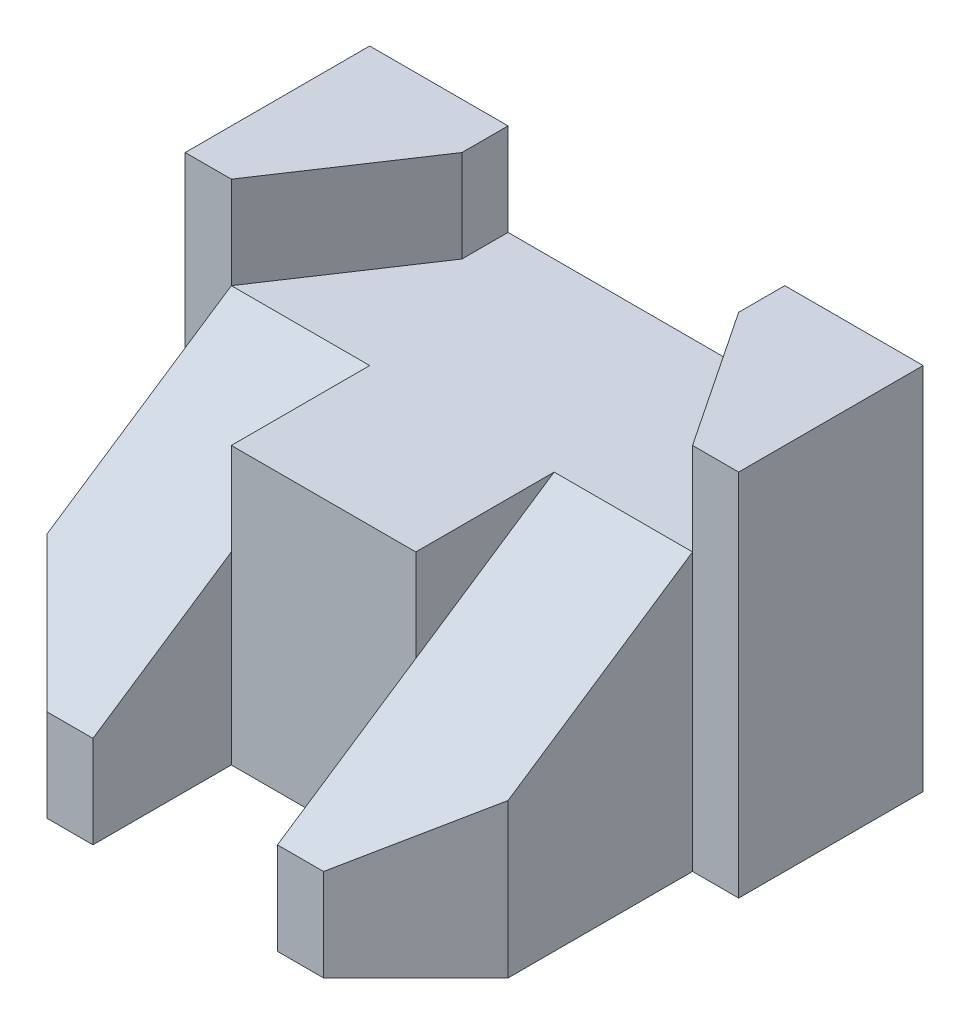
SolidWorks part; units mm, degrees
ref_plane "Front Plane" through (0, 0, 0) normal (0, 0, 1) x (1, 0, 0)
ref_plane "Top Plane" through (0, 0, 0) normal (0, 1, 0) x (1, 0, 0)
ref_plane "Right Plane" through (0, 0, 0) normal (1, 0, 0) x (0, 0, -1)
sketch "Sketch1" plane through (0, 0, 0) normal (0, 1, 0) x (1, 0, 0)
  line L1 (0, 0) -> (120, 0)
  line L2 (0, 0) -> (0, 100)
  line L3 (0, 100) -> (120, 100)
  line L4 (120, 0) -> (120, 100)
  dimension "D1" = 120
  dimension "D2" = 100
extrude "Boss-Extrude1" add sketch "Sketch1" along normal blind 80
sketch "Sketch2" plane through (0, 80, 0) normal (0, 1, 0) x (1, 0, 0)
  line L0 (0, 0) -> (120, 0) construction
  line L1 (80, 0) -> (40, 0)
  line L2 (80, 0) -> (80, 30)
  line L3 (80, 30) -> (40, 30)
  line L4 (40, 0) -> (40, 30)
  dimension "D1" = 40
  dimension "D2" = 30
  dimension "D3" = 40
extrude "Cut-Extrude1" cut sketch "Sketch2" against normal blind 80
sketch "Sketch3" plane through (0, 80, 0) normal (0, 1, 0) x (1, 0, 0)
  line L0 (0, 60) -> (10, 60)
  line L1 (0, 100) -> (0, 0) construction
  line L2 (10, 60) -> (10, 20)
  line L3 (10, 20) -> (30, 0)
  line L4 (0, 0) -> (40, 0) construction
  line L5 (30, 0) -> (0, 0)
  line L6 (0, 0) -> (0, 60)
  line L7 (120, 60) -> (110, 60)
  line L8 (120, 0) -> (120, 100) construction
  line L9 (110, 60) -> (110, 20)
  line L10 (110, 20) -> (90, 0)
  line L11 (80, 0) -> (120, 0) construction
  line L12 (90, 0) -> (120, 0)
  line L13 (120, 0) -> (120, 60)
  dimension "D1" = 10
  dimension "D2" = 40
  dimension "D3" = 60
  dimension "D4" = 20
  dimension "D5" = 20
  dimension "D6" = 10
  dimension "D7" = 40
  dimension "D8" = 20
  dimension "D9" = 20
  dimension "D10" = 10
extrude "Cut-Extrude2" cut sketch "Sketch3" against normal blind 80
sketch "Sketch4" plane through (0, 80, 0) normal (0, 1, 0) x (1, 0, 0)
  line L0 (30, 100) -> (90, 100)
  line L1 (120, 100) -> (0, 100) construction
  line L2 (90, 100) -> (90, 90)
  line L3 (40, 60) -> (10.001, 60)
  line L4 (10.001, 60) -> (30, 90)
  line L5 (80, 60) -> (80, 30)
  line L6 (80, 30) -> (40, 30)
  line L7 (40, 30) -> (40, 60)
  line L8 (80, 60) -> (109.999, 60)
  line L9 (109.999, 60) -> (90, 90)
  line L10 (30, 90) -> (30, 100)
  dimension "D1" = 30
  dimension "D2" = 30
  dimension "D3" = 10
  dimension "D4" = 10
  dimension "D5" = 29.999
  dimension "D6" = 29.999
  dimension "D7" = 19.999
  dimension "D8" = 30
  dimension "D9" = 30
extrude "Cut-Extrude6" cut sketch "Sketch4" against normal blind 20
sketch "Sketch5" plane through (0, 0, -60) normal (0, 0, -1) x (-1, 0, 0)
  line L1 (-109.999, 80) -> (-80, 80)
  line L2 (-109.999, 80) -> (-109.999, 60)
  line L3 (-109.999, 60) -> (-80, 60)
  line L4 (-80, 80) -> (-80, 60)
  line L5 (-40, 80) -> (-10.001, 80)
  line L6 (-40, 80) -> (-40, 60)
  line L7 (-40, 60) -> (-10.001, 60)
  line L8 (-10.001, 80) -> (-10.001, 60)
extrude "Cut-Extrude7" cut sketch "Sketch5" against normal blind 68
sketch "Sketch6" plane through (109.999, 0, 0) normal (-1, 0, 0) x (0, 0, 1)
  line L1 (-60, 80) -> (-19.999, 80)
  line L2 (-60, 80) -> (-60, 60)
  line L3 (-60, 60) -> (-19.999, 60)
  line L4 (-19.999, 80) -> (-19.999, 60)
extrude "Cut-Extrude8" cut sketch "Sketch6" against normal blind 68
sketch "Sketch7" plane through (10.001, 0, 0) normal (1, 0, 0) x (0, 0, -1)
  line L1 (60, 60) -> (19.999, 60)
  line L2 (60, 60) -> (60, 80)
  line L3 (60, 80) -> (19.999, 80)
  line L4 (19.999, 60) -> (19.999, 80)
extrude "Cut-Extrude9" cut sketch "Sketch7" against normal blind 68
sketch "Sketch8" plane through (0, 0, 0) normal (0, 0, 1) x (1, 0, 0)
  line L0 (40, 0) -> (40, 60) construction
  point P0 (40, 20)
  dimension "D1" = 20
sketch "Sketch9" plane through (0, 60, 0) normal (0, 1, 0) x (1, 0, 0)
  point P0 (40.001, 60)
  dimension "D1" = 30
  dimension "D2" = 30
ref_plane "Plane1" through (0, 13.8462, 9.2308) normal (0, 0.8321, 0.5547) x (1, 0, 0)
sketch "Sketch10" plane through (0, 13.8462, 9.2308) normal (0, 0.8321, 0.5547) x (1, 0, 0)
  line L0 (40.001, 83.205) -> (40, 11.094)
  line L1 (40, 11.094) -> (10, 11.094)
  line L2 (10, 11.094) -> (10, 83.205)
  line L3 (10, 83.205) -> (40.001, 83.205)
extrude "Cut-Extrude10" cut sketch "Sketch10" along normal blind 68
sketch "Sketch11" plane through (0, 60, 0) normal (0, 1, 0) x (1, 0, 0)
  point P0 (80, 60)
  dimension "D1" = 30
  dimension "D2" = 30
sketch "Sketch12" plane through (0, 0, 0) normal (0, 0, 1) x (1, 0, 0)
  line L0 (80, 0) -> (80, 60) construction
  point P0 (80, 20)
  dimension "D1" = 20
ref_plane "Plane2" through (0, 13.8462, 9.2308) normal (0, -0.8321, -0.5547) x (-1, 0, 0)
sketch "Sketch13" plane through (0, 13.8462, 9.2308) normal (0, -0.8321, -0.5547) x (-1, 0, 0)
  line L0 (-80, 83.205) -> (-109.999, 83.205)
  line L1 (-109.999, 83.205) -> (-109.999, 11.094)
  line L2 (-109.999, 11.094) -> (-80, 11.094)
  line L3 (-80, 11.094) -> (-80, 83.205)
extrude "Cut-Extrude11" cut sketch "Sketch13" against normal blind 68
sketch "Sketch14" plane through (109.999, 0, 0) normal (-1, 0, 0) x (0, 0, 1)
  line L0 (-60, 60) -> (-19.999, 33.3327)
  line L1 (-19.999, 33.3327) -> (-19.999, 60)
  line L2 (-19.999, 60) -> (-60, 60)
extrude "Cut-Extrude12" cut sketch "Sketch14" against normal blind 68
